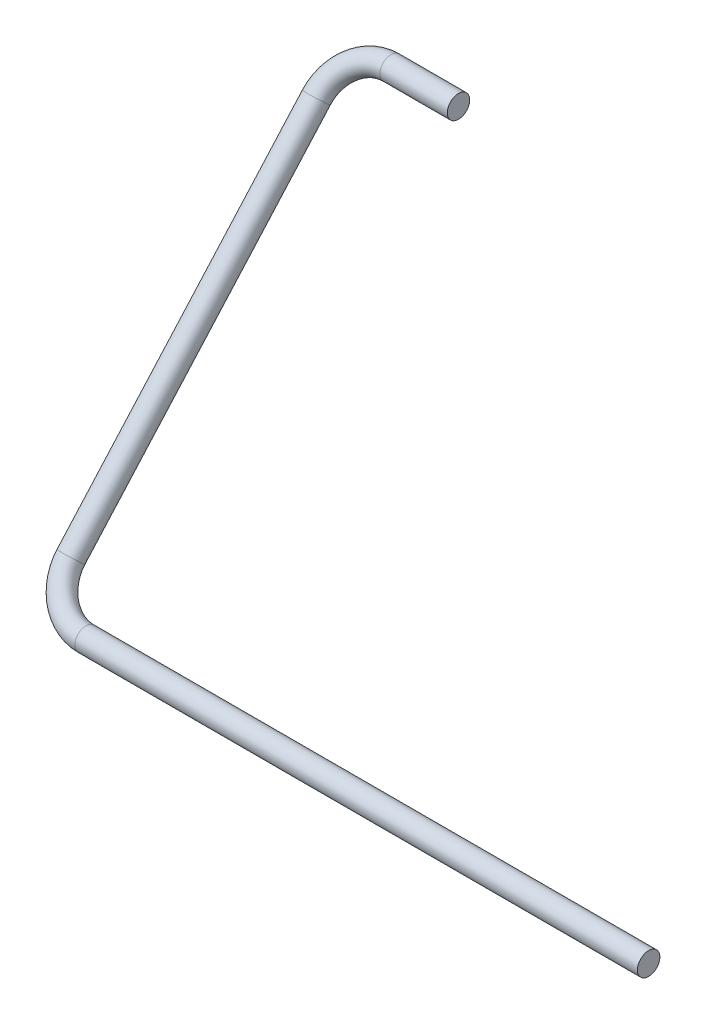
SolidWorks part; units mm, degrees
ref_plane "Front Plane" through (0, 0, 0) normal (0, 0, 1) x (1, 0, 0)
ref_plane "Top Plane" through (0, 0, 0) normal (0, 1, 0) x (1, 0, 0)
ref_plane "Right Plane" through (0, 0, 0) normal (1, 0, 0) x (0, 0, -1)
sketch3d "3DSketch1"
  line L0 (-635.0405, 1805.0326, -106.3068) -> (-673.1405, 1805.0326, -106.3068)
  line L1 (-713.463, 1805.0326, -106.3068) -> (-558.396, 1805.0326, -106.3068) construction
  line L2 (-583.1455, 1805.0326, -106.3068) -> (-627.9905, 1805.0326, -106.3068) construction
  line L3 (-354.8785, 1611.503, 66.2784) -> (-673.1405, 1611.503, 66.2784)
  line L4 (-354.688, 1611.503, 66.2784) -> (-336.8683, 1611.503, 66.2784) construction
  line L6 (-698.5405, 1786.0756, -89.4014) -> (-698.5405, 1630.46, 49.373)
  arc A1 (-673.1405, 1805.0326, -106.3068) -> (-698.5405, 1786.0756, -89.4014) centre (-673.1405, 1786.0756, -89.4014) ccw
  arc A2 (-673.1405, 1611.503, 66.2784) -> (-698.5405, 1630.46, 49.373) centre (-673.1405, 1630.46, 49.373) ccw
  point P10 (-703.3199, 1611.503, 72.7567)
  point P11 (0, 0, 0)
  point P14 (-698.5405, 1805.0326, -106.3068)
  point P15 (-673.1405, 1802.981, -70.4444)
  point P18 (-698.5405, 1611.503, 66.2784)
  point P19 (-673.1405, 1613.5546, 30.416)
  point P20 (-414.3442, 1611.503, 67.8228)
  point P21 (0, 0, 0)
  dimension "D2" = 25.4
  dimension "D1" = 63.5
sweep "Sweep1" add path "3DSketch1" circular profile diameter 12.7 parameters "D3"=12.7
ref_plane "Plane1" through (0, 746.7858, 837.4132) normal (0, 0.6656, 0.7463) x (1, 0, 0)
